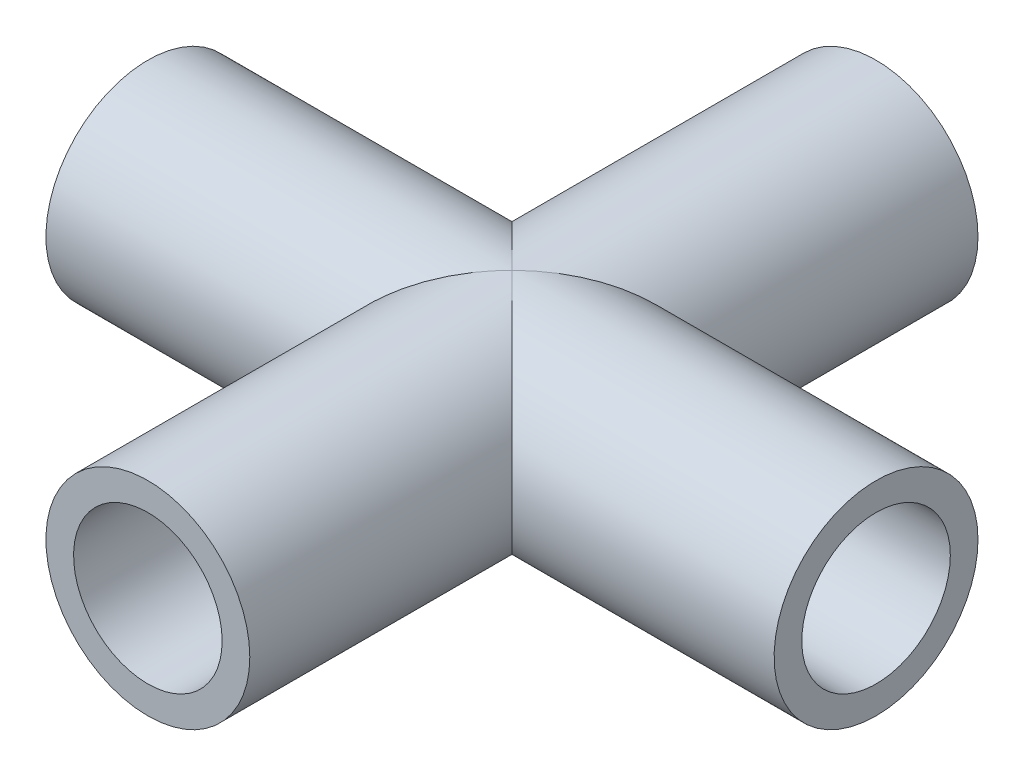
SolidWorks part; units mm, degrees
material "PVC Rigid"
ref_plane "Front Plane" through (0, 0, 0) normal (0, 0, 1) x (1, 0, 0)
ref_plane "Top Plane" through (0, 0, 0) normal (0, 1, 0) x (1, 0, 0)
ref_plane "Right Plane" through (0, 0, 0) normal (1, 0, 0) x (0, 0, -1)
sketch "Sketch1" plane through (0, 0, 0) normal (0, 0, 1) x (1, 0, 0)
  circle A0 centre (0, 0) radius 8.89
  circle A1 centre (0, 0) radius 6.477
  dimension "D1" = 17.78
  dimension "D2" = 12.954
extrude "Boss-Extrude1" add sketch "Sketch1" along normal blind 63.5
sketch "Sketch2" plane through (0, 0, 0) normal (1, 0, 0) x (0, 0, -1)
  line L0 (-31.75, 8.89) -> (-31.75, -8.89) construction
  line L1 (0, 8.89) -> (-63.5, 8.89) construction
  line L2 (-63.5, -8.89) -> (0, -8.89) construction
  line L3 (-63.5, 0) -> (0, 0) construction
  line L4 (-63.5, 8.89) -> (-63.5, -8.89) construction
  circle A0 centre (-31.75, 0) radius 8.89
  circle A1 centre (-31.75, 0) radius 6.477
  dimension "D1" = 17.78
  dimension "D2" = 12.954
extrude "Boss-Extrude2" add sketch "Sketch2" along normal mid plane 63.5
sketch "Sketch4" plane through (0, 0, 0) normal (0, 0, -1) x (-1, 0, 0)
  circle A0 centre (0, 0) radius 6.477
extrude "Cut-Extrude1" cut sketch "Sketch4" against normal through all
sketch "Sketch5" plane through (31.75, 0, 0) normal (1, 0, 0) x (0, 0, -1)
  circle A0 centre (-31.75, 0) radius 6.477
extrude "Cut-Extrude2" cut sketch "Sketch5" against normal through all
